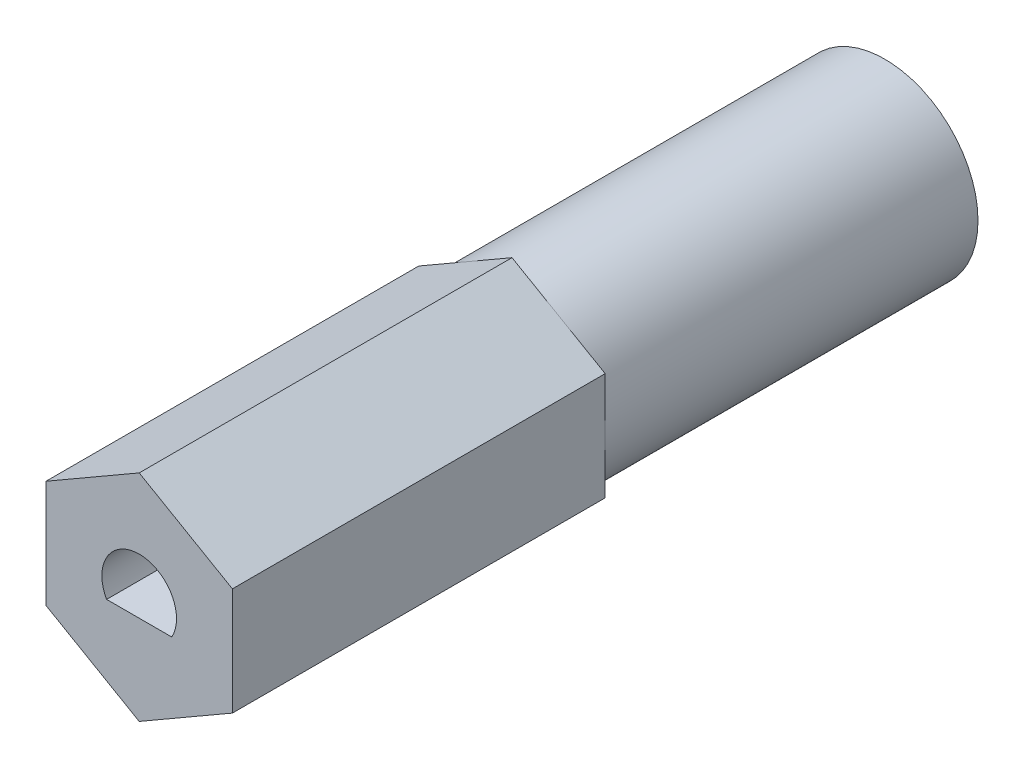
SolidWorks part; units mm, degrees
ref_plane "Front Plane" through (0, 0, 0) normal (0, 0, 1) x (1, 0, 0)
ref_plane "Top Plane" through (0, 0, 0) normal (0, 1, 0) x (1, 0, 0)
ref_plane "Right Plane" through (0, 0, 0) normal (1, 0, 0) x (0, 0, -1)
sketch "Sketch1" plane through (0, 0, 0) normal (0, 0, 1) x (1, 0, 0)
  line L1 (0, 3.6662) -> (-3.175, 1.8331)
  line L2 (-3.175, 1.8331) -> (-3.175, -1.8331)
  line L3 (-3.175, -1.8331) -> (0, -3.6662)
  line L4 (0, -3.6662) -> (3.175, -1.8331)
  line L5 (3.175, -1.8331) -> (3.175, 1.8331)
  line L6 (3.175, 1.8331) -> (0, 3.6662)
  circle A0 centre (0, 0) radius 3.175
  circle A1 centre (0, 0) radius 3.175 construction
  dimension "D1" = 6.35
extrude "Boss-Extrude1" add sketch "Sketch1" against normal blind 25.4 contours L1 L2 L3 L4 L5 L6
sketch "Sketch2" plane through (0, 0, 0) normal (0, 0, 1) x (1, 0, 0)
  line L0 (-1.1099, -0.6207) -> (1.1099, -0.6207)
  arc A0 (1.1099, -0.6207) -> (-1.1099, -0.6207) centre (0, 0) ccw
  dimension "D1" = 1.2716
  dimension "D2" = 1.8923
extrude "Cut-Extrude1" cut sketch "Sketch2" against normal blind 5.08
ref_plane "Plane1" through (0, 0, -12.7) normal (0, 0, 1) x (1, 0, 0)
sketch "Sketch3" plane through (0, 0, -12.7) normal (0, 0, 1) x (1, 0, 0)
  circle A0 centre (0, 0) radius 3.175
  dimension "D1" = 6.35
extrude "Cut-Extrude2" cut sketch "Sketch3" against normal through all flip side to cut
